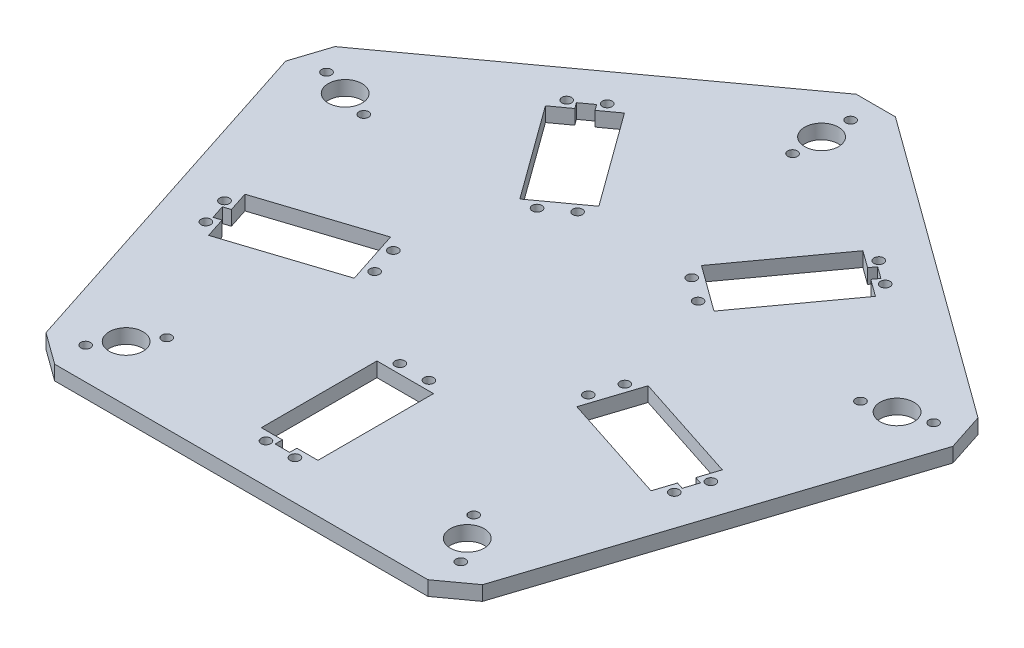
SolidWorks part; units mm, degrees
ref_plane "Plan de face" through (0, 0, 0) normal (0, 0, 1) x (1, 0, 0)
ref_plane "Plan de dessus" through (0, 0, 0) normal (0, 1, 0) x (1, 0, 0)
ref_plane "Plan de droite" through (0, 0, 0) normal (1, 0, 0) x (0, 0, -1)
sketch "Esquisse2" plane through (0, 0, 0) normal (0, 1, 0) x (1, 0, 0)
  line L0 (0, 0) -> (0, -80.2728) construction
  line L1 (70.5342, 22.918) -> (0, 74.1641)
  line L2 (0, 74.1641) -> (-70.5342, 22.918)
  line L3 (-70.5342, 22.918) -> (-43.5926, -60)
  line L4 (-43.5926, -60) -> (43.5926, -60)
  line L5 (43.5926, -60) -> (70.5342, 22.918)
  line L6 (-5.85, -26.1) -> (5.85, -26.1)
  line L7 (-5.85, -26.1) -> (-5.85, -50)
  line L8 (-5.85, -50) -> (-1.5, -50)
  line L9 (5.85, -26.1) -> (5.85, -50)
  line L10 (-23.0148, -13.629) -> (-45.7451, -21.0145)
  line L11 (-26.6303, -2.5017) -> (-49.3606, -9.8872)
  line L12 (-26.6303, -2.5017) -> (-23.0148, -13.629)
  line L13 (-49.3606, -9.8872) -> (-48.0164, -14.0243)
  line L14 (-47.0893, -16.8774) -> (-45.7451, -21.0145)
  line L15 (-48.5159, -17.341) -> (-47.0893, -16.8774)
  line L16 (-49.4429, -14.4878) -> (-48.5159, -17.341)
  line L17 (-48.0164, -14.0243) -> (-49.4429, -14.4878)
  line L18 (-20.0739, 17.6768) -> (-34.122, 37.0123)
  line L19 (-10.6084, 24.5539) -> (-24.6565, 43.8894)
  line L20 (-10.6084, 24.5539) -> (-20.0739, 17.6768)
  line L21 (-24.6565, 43.8894) -> (-28.1757, 41.3325)
  line L22 (-30.6028, 39.5692) -> (-34.122, 37.0123)
  line L23 (-31.4845, 40.7827) -> (-30.6028, 39.5692)
  line L24 (-29.0574, 42.5461) -> (-31.4845, 40.7827)
  line L25 (-28.1757, 41.3325) -> (-29.0574, 42.5461)
  line L26 (-70.5342, 22.918) -> (0, 0) construction
  line L27 (-57.0634, 18.541) -> (-59.0076, 12.5574) construction
  line L28 (-5.85, -38.05) -> (5.85, -38.05) construction
  line L29 (-1.5, -50) -> (-1.5, -51.5)
  line L30 (-1.5, -51.5) -> (1.5, -51.5)
  line L31 (1.5, -51.5) -> (1.5, -50)
  line L32 (10.6084, 24.5539) -> (24.6565, 43.8894)
  line L33 (20.0739, 17.6768) -> (34.122, 37.0123)
  line L34 (20.0739, 17.6768) -> (10.6084, 24.5539)
  line L35 (34.122, 37.0123) -> (30.6028, 39.5692)
  line L36 (28.1757, 41.3325) -> (24.6565, 43.8894)
  line L37 (29.0574, 42.5461) -> (28.1757, 41.3325)
  line L38 (31.4845, 40.7827) -> (29.0574, 42.5461)
  line L39 (30.6028, 39.5692) -> (31.4845, 40.7827)
  line L40 (26.6303, -2.5017) -> (49.3606, -9.8872)
  line L41 (23.0148, -13.629) -> (45.7451, -21.0145)
  line L42 (23.0148, -13.629) -> (26.6303, -2.5017)
  line L43 (45.7451, -21.0145) -> (47.0893, -16.8774)
  line L44 (1.5, -50) -> (5.85, -50)
  line L45 (48.0164, -14.0243) -> (49.3606, -9.8872)
  line L46 (49.4429, -14.4878) -> (48.0164, -14.0243)
  line L47 (48.5159, -17.341) -> (49.4429, -14.4878)
  line L48 (47.0893, -16.8774) -> (48.5159, -17.341)
  circle A0 centre (-57.0634, 18.541) radius 3.5
  circle A1 centre (0, 0) radius 60 construction
  circle A2 centre (0, 60) radius 3.5
  circle A3 centre (57.0634, 18.541) radius 3.5
  circle A4 centre (35.2671, -48.541) radius 3.5
  circle A5 centre (-35.2671, -48.541) radius 3.5
  circle A6 centre (-62.7697, 20.3951) radius 1
  circle A7 centre (-51.3571, 16.6869) radius 1
  circle A8 centre (0, 66) radius 1
  circle A9 centre (0, 54) radius 1
  circle A10 centre (62.7697, 20.3951) radius 1
  circle A11 centre (51.3571, 16.6869) radius 1
  circle A12 centre (38.7938, -53.3951) radius 1
  circle A13 centre (31.7404, -43.6869) radius 1
  circle A14 centre (-38.7938, -53.3951) radius 1
  circle A15 centre (-31.7404, -43.6869) radius 1
  circle A16 centre (-3, -51.9) radius 1
  circle A17 centre (3, -51.9) radius 1
  circle A18 centre (3, -24.2) radius 1
  circle A19 centre (-3, -24.2) radius 1
  circle A20 centre (-23.9426, -4.625) radius 1
  circle A21 centre (-22.0885, -10.3314) radius 1
  circle A22 centre (-48.4328, -18.8912) radius 1
  circle A23 centre (-50.2869, -13.1848) radius 1
  circle A24 centre (-11.7974, 21.3416) radius 1
  circle A25 centre (-16.6515, 17.8149) radius 1
  circle A26 centre (-32.9331, 40.2246) radius 1
  circle A27 centre (-28.079, 43.7513) radius 1
  circle A28 centre (16.6515, 17.8149) radius 1
  circle A29 centre (11.7974, 21.3416) radius 1
  circle A30 centre (28.079, 43.7513) radius 1
  circle A31 centre (32.9331, 40.2246) radius 1
  circle A32 centre (22.0885, -10.3314) radius 1
  circle A33 centre (23.9426, -4.625) radius 1
  circle A34 centre (50.2869, -13.1848) radius 1
  circle A35 centre (48.4328, -18.8912) radius 1
  point P32 (0, 0)
  point P43 (0, 0)
  point P65 (0, 0)
  point P69 (-5.85, -38.05)
  point P74 (0, -26.1)
  point P109 (0, 0)
  point P112 (0, -51.5)
  point P132 (0, 0)
  point P133 (0, 0)
  dimension "D1" = 120
  dimension "D6" = 5
  dimension "D7" = 7
  dimension "D8" = 5
  dimension "D9" = 2
  dimension "D10" = 6
  dimension "D11" = 5
  dimension "D12" = 2
  dimension "D13" = 1.9
  dimension "D14" = 3
  dimension "D2" = 23.9
  dimension "D3" = 11.7
  dimension "D4" = 10
  dimension "D5" = 1.5
  dimension "D16" = 3
  dimension "D15" = 5
extrude "Boss.-Extru.1" add sketch "Esquisse2" along normal blind 3
chamfer "Chanfrein2" distance 5 5 edges at (70.5342, 1.5, -22.918) (0, 1.5, -74.1641) (-70.5342, 1.5, -22.918) (-43.5926, 1.5, 60) (43.5926, 1.5, 60)
